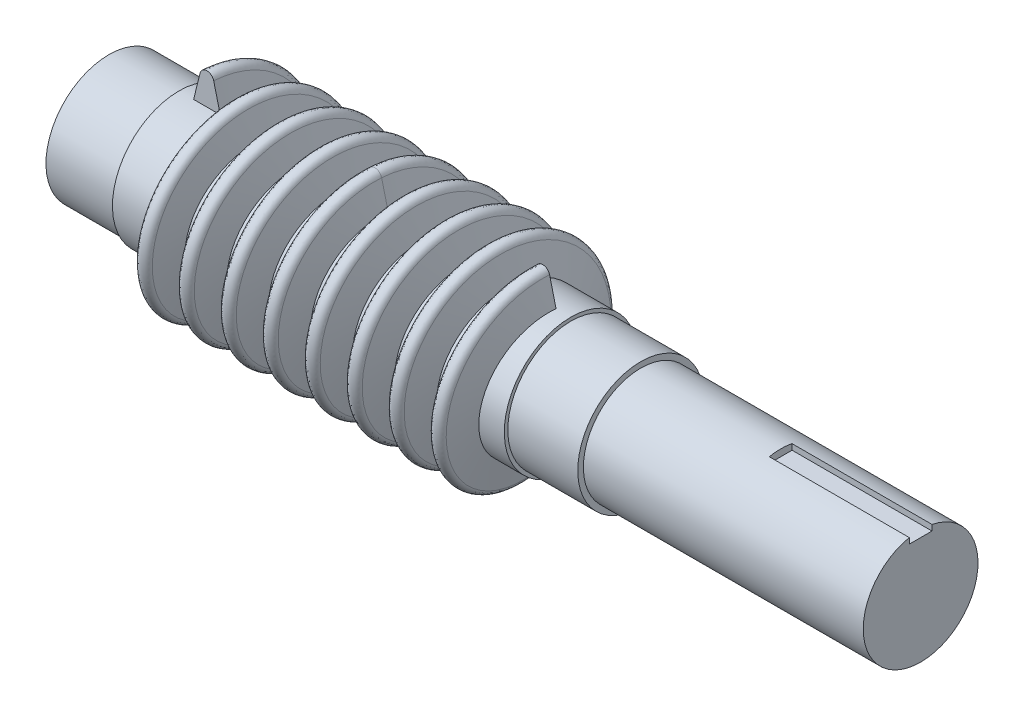
SolidWorks part; units mm, degrees
material "1023 Carbon Steel Sheet (SS)"
ref_plane "Front Plane" through (0, 0, 0) normal (0, 0, 1) x (1, 0, 0)
ref_plane "Top Plane" through (0, 0, 0) normal (0, 1, 0) x (1, 0, 0)
ref_plane "Right Plane" through (0, 0, 0) normal (1, 0, 0) x (0, 0, -1)
sketch "Sketch1" plane through (0, 0, 0) normal (0, 0, 1) x (1, 0, 0)
  line L0 (78, -11.75) -> (-38, -11.75)
  line L1 (-38, -11.75) -> (-38, -2.75)
  line L2 (-38, -2.75) -> (-28, -2.75)
  line L3 (-28, -2.75) -> (-28, -2.25)
  line L4 (-28, -2.25) -> (28, -2.25)
  line L5 (28, -2.25) -> (28, -2.75)
  line L6 (28, -2.75) -> (38, -2.75)
  line L7 (38, -2.75) -> (38, -3.55)
  line L8 (38, -3.55) -> (78, -3.55)
  line L9 (78, -3.55) -> (78, -11.75)
  dimension "D1" = 116
  dimension "D2" = 9
  dimension "D3" = 8.2
  dimension "D4" = 10
  dimension "D5" = 40
  dimension "D6" = 10
  dimension "D7" = 56
  dimension "D8" = 9.5
  dimension "D9" = 9
  dimension "D10" = 38
  dimension "D11" = 11.75
revolve "Revolve1" add sketch "Sketch1" angle 360 about L0
sketch "Sketch2" plane through (0, 0, 0) normal (1, 0, 0) x (0, 0, -1)
  circle A0 centre (0, -11.75) radius 9.5 construction
  circle A1 centre (0, -11.75) radius 9.5
curve "Helix/Spiral1" pitch 6 height 24 turns 4
sketch "Sketch3" plane through (0, 0, 0) normal (0, 0, 1) x (1, 0, 0)
  line L0 (0, -2.25) -> (0, 1.25) construction
  line L1 (28, -2.25) -> (-28, -2.25) construction
  line L2 (-0.9705, 1.4911) -> (-1.9, -2.25)
  line L3 (-1.9, -2.25) -> (-1.9, -2.95)
  line L4 (0.9705, 1.4911) -> (1.9, -2.25)
  line L5 (1.9, -2.25) -> (1.9, -2.95)
  line L6 (-1.9, -2.95) -> (1.9, -2.95)
  arc A0 (0.9705, 1.4911) -> (-0.9705, 1.4911) centre (0, 1.25) ccw
  dimension "D2" = 2
  dimension "D1" = 3.5
  dimension "D3" = 3.8
  dimension "D4" = 0.7
sweep "Sweep1" add profiles "Sketch3" path "Helix/Spiral1"
sketch "Sketch4" plane through (0, 0, 0) normal (1, 0, 0) x (0, 0, -1)
  circle A0 centre (0, -11.75) radius 9.5 construction
  circle A1 centre (0, -11.75) radius 9.5
curve "Helix/Spiral2" pitch 6 height 24 turns 4
sketch "Sketch6" plane through (0, 0, 0) normal (0, 0, 1) x (1, 0, 0)
  line L5 (-0.9705, 1.4911) -> (-1.9, -2.25)
  line L6 (-1.9, -2.25) -> (-1.9, -2.95)
  line L7 (-1.9, -2.95) -> (1.9, -2.95)
  line L8 (1.9, -2.95) -> (1.9, -2.25)
  line L9 (1.9, -2.25) -> (0.9705, 1.4911)
  line L10 (-0.9705, 1.4911) -> (-1.9, -2.25)
  line L11 (-1.9, -2.25) -> (-1.9, -2.95)
  line L12 (-1.9, -2.95) -> (1.9, -2.95)
  line L13 (1.9, -2.95) -> (1.9, -2.25)
  line L14 (1.9, -2.25) -> (0.9705, 1.4911)
  arc A1 (0.9705, 1.4911) -> (-0.9705, 1.4911) centre (0, 1.25) ccw
  arc A2 (0.9705, 1.4911) -> (-0.9705, 1.4911) centre (0, 1.25) ccw
  dimension "D1" = 0
sweep "Sweep2" add profiles "Sketch6" path "Helix/Spiral2"
sketch "Sketch7" plane through (78, 0, 0) normal (1, 0, 0) x (0, 0, -1)
  line L0 (0, -11.75) -> (4.8922, -11.75) construction
  line L1 (0, -11.75) -> (0, -0.812) construction
  line L2 (-1.625, -4.53) -> (1.625, -4.53)
  line L3 (-1.625, -4.53) -> (-1.625, -3.03)
  line L4 (-1.625, -3.03) -> (1.625, -3.03)
  line L5 (1.625, -4.53) -> (1.625, -3.03)
  line L6 (0, 1.4911) -> (0, -2.25) construction
  dimension "D1" = 3.25
  dimension "D2" = 1.5
  dimension "D3" = 7.22
extrude "Cut-Extrude1" cut sketch "Sketch7" against normal blind 20
sketch "Sketch8" plane through (-38, 0, 0) normal (-1, 0, 0) x (0, 0, 1)
  line L2 (-9, -11.75) -> (9, -11.75) construction
  circle A0 centre (0, -11.75) radius 9 construction
ref_plane "Plane1" through (0, -11.75, 0) normal (0, 1, 0) x (1, 0, 0)
scale "Scale1" scale about centroid uniform scaling yes scale factor 0.5
